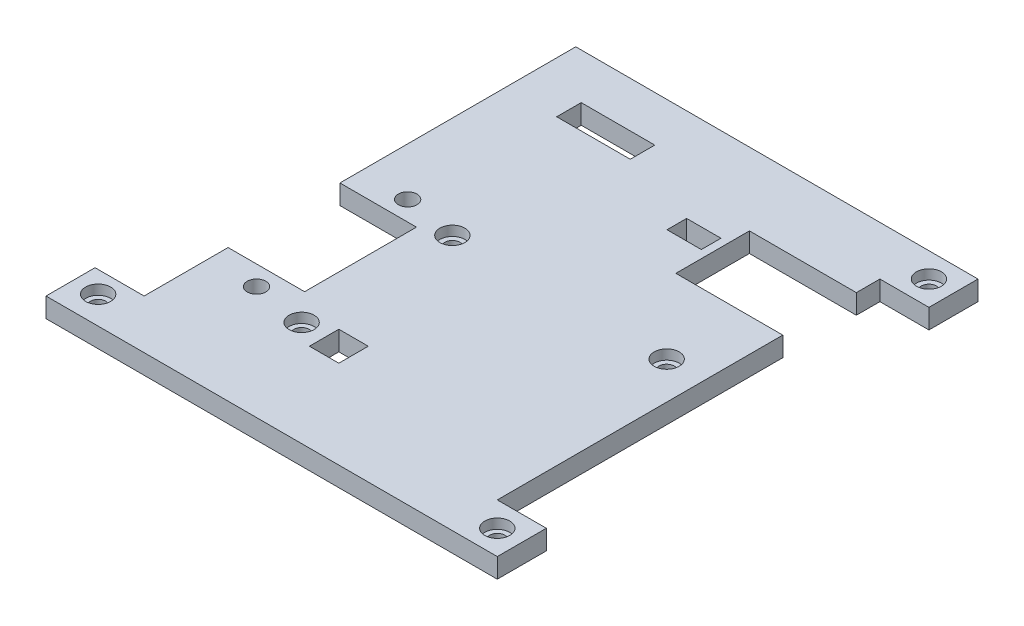
SolidWorks part; units mm, degrees
ref_plane "Спереди" through (0, 0, 0) normal (0, 0, 1) x (1, 0, 0)
ref_plane "Сверху" through (0, 0, 0) normal (0, 1, 0) x (1, 0, 0)
ref_plane "Справа" through (0, 0, 0) normal (1, 0, 0) x (0, 0, -1)
sketch "Sketch1" plane through (0, 0, 0) normal (0, 1, 0) x (1, 0, 0)
  line L0 (32.4854, 9.094) -> (23.5854, 9.094)
  line L1 (0.4854, 14.494) -> (32.4854, 14.494)
  line L2 (0.4854, 14.494) -> (0.4854, -7.5459)
  line L3 (0.4854, -30.506) -> (32.4854, -30.506)
  line L4 (32.4854, 14.494) -> (32.4854, 9.094)
  line L5 (11.3414, -23.5133) -> (14.3414, -23.5133)
  line L6 (11.3414, -23.5133) -> (11.3414, -20.5133)
  line L7 (11.3414, -20.5133) -> (14.3414, -20.5133)
  line L8 (14.3414, -23.5133) -> (14.3414, -20.5133)
  line L9 (23.5854, 9.094) -> (23.5854, 1.594)
  line L10 (23.5854, 1.594) -> (32.4854, 1.594)
  line L11 (32.4854, 1.594) -> (32.4854, -30.506)
  line L12 (0.4854, -18.9459) -> (0.4854, -30.506)
  line L13 (0.4854, -7.5459) -> (6.2854, -7.5459)
  line L15 (0.4854, -18.9459) -> (6.2854, -18.9459)
  line L16 (6.2854, -7.5459) -> (6.2854, -18.9459)
  line L18 (22.7854, 6.994) -> (19.2854, 6.994)
  line L19 (22.7854, 6.994) -> (22.7854, 4.994)
  line L20 (22.7854, 4.994) -> (19.2854, 4.994)
  line L21 (19.2854, 6.994) -> (19.2854, 4.994)
  line L22 (3.6896, 11.844) -> (11.1896, 11.844)
  line L23 (3.6896, 11.844) -> (3.6896, 9.344)
  line L24 (3.6896, 9.344) -> (11.1896, 9.344)
  line L25 (11.1896, 11.844) -> (11.1896, 9.344)
  circle A0 centre (30.6854, -6.439) radius 0.775
  circle A1 centre (8.8414, -6.439) radius 0.775
  circle A2 centre (8.8414, -21.806) radius 0.775
  circle A3 centre (3.3854, -5.5459) radius 0.95
  circle A4 centre (3.3854, -20.9459) radius 0.95
  dimension "D6" = 1.55
  dimension "D16" = 1.9
  dimension "D1" = 45
  dimension "D2" = 32
  dimension "D3" = 1.8
  dimension "D4" = 21.844
  dimension "D5" = 15.367
  dimension "D7" = 8.7
  dimension "D8" = 3
  dimension "D9" = 3
  dimension "D10" = 2.5
  dimension "D11" = 5.4
  dimension "D12" = 7.5
  dimension "D13" = 8.9
  dimension "D14" = 11.4
  dimension "D15" = 5.8
  dimension "D17" = 2
  dimension "D18" = 2
  dimension "D19" = 2.9
  dimension "D20" = 2.9
  dimension "D21" = 0.8
  dimension "D22" = 3.5
  dimension "D23" = 2
  dimension "D24" = 3.4
  dimension "D25" = 7.5
  dimension "D26" = 2.5
  dimension "D27" = 2.65
extrude "Boss-Extrude1" add sketch "Sketch1" along normal blind 2
sketch "Sketch2" plane through (0, 2, 0) normal (0, 1, 0) x (1, 0, 0)
  circle A0 centre (8.8414, -6.439) radius 1.275
  circle A1 centre (30.6854, -6.439) radius 1.275
  circle A2 centre (8.8414, -21.806) radius 1.275
  dimension "D1" = 2.55
extrude "Cut-Extrude1" cut sketch "Sketch2" against normal blind 1
sketch "Sketch4" plane through (0.4854, 0, 0) normal (-1, 0, 0) x (0, 0, 1)
  line L1 (-14.494, 2) -> (7.5459, 2)
  line L2 (-14.494, 2) -> (-14.494, 0)
  line L3 (-14.494, 0) -> (7.5459, 0)
  line L4 (7.5459, 2) -> (7.5459, 0)
  line L5 (18.9459, 0) -> (30.506, 0)
  line L6 (18.9459, 0) -> (18.9459, 2)
  line L7 (18.9459, 2) -> (30.506, 2)
  line L8 (30.506, 0) -> (30.506, 2)
extrude "Boss-Extrude3" add sketch "Sketch4" along normal blind 2
sketch "Sketch5" plane through (32.4854, 0, 0) normal (1, 0, 0) x (0, 0, -1)
  line L1 (14.494, 0) -> (9.094, 0)
  line L2 (14.494, 0) -> (14.494, 2)
  line L3 (14.494, 2) -> (9.094, 2)
  line L4 (9.094, 0) -> (9.094, 2)
  line L5 (1.594, 2) -> (-30.506, 2)
  line L6 (1.594, 2) -> (1.594, 0)
  line L7 (1.594, 0) -> (-30.506, 0)
  line L8 (-30.506, 2) -> (-30.506, 0)
extrude "Boss-Extrude4" add sketch "Sketch5" along normal blind 2
sketch "Sketch6" plane through (0, 0, -14.494) normal (0, 0, -1) x (-1, 0, 0)
  line L1 (-34.4854, 0) -> (1.5146, 0)
  line L2 (-34.4854, 0) -> (-34.4854, 2)
  line L3 (-34.4854, 2) -> (1.5146, 2)
  line L4 (1.5146, 0) -> (1.5146, 2)
extrude "Boss-Extrude5" add sketch "Sketch6" along normal blind 2
sketch "Sketch7" plane through (0, 0, 30.506) normal (0, 0, 1) x (1, 0, 0)
  line L1 (-1.5146, 0) -> (34.4854, 0)
  line L2 (-1.5146, 0) -> (-1.5146, 2)
  line L3 (-1.5146, 2) -> (34.4854, 2)
  line L4 (34.4854, 0) -> (34.4854, 2)
extrude "Boss-Extrude6" add sketch "Sketch7" along normal blind 2
sketch "Sketch8" plane through (34.4854, 0, 0) normal (1, 0, 0) x (0, 0, -1)
  line L0 (9.094, 0) -> (16.494, 0) construction
  line L1 (16.494, 2) -> (11.494, 2)
  line L2 (16.494, 2) -> (16.494, 0)
  line L3 (16.494, 0) -> (11.494, 0)
  line L4 (11.494, 2) -> (11.494, 0)
  line L5 (1.594, 2) -> (-32.506, 2) construction
  line L6 (-32.506, 0) -> (-27.506, 0)
  line L7 (-32.506, 0) -> (-32.506, 2)
  line L8 (-32.506, 2) -> (-27.506, 2)
  line L9 (-27.506, 0) -> (-27.506, 2)
  dimension "D1" = 5
extrude "Boss-Extrude7" add sketch "Sketch8" along normal blind 5
sketch "Sketch9" plane through (-1.5146, 0, 0) normal (-1, 0, 0) x (0, 0, 1)
  line L0 (32.506, 2) -> (18.9459, 2) construction
  line L1 (32.506, 0) -> (27.506, 0)
  line L2 (32.506, 0) -> (32.506, 2)
  line L3 (32.506, 2) -> (27.506, 2)
  line L4 (27.506, 0) -> (27.506, 2)
  dimension "D1" = 5
extrude "Boss-Extrude8" add sketch "Sketch9" along normal blind 5
sketch "Sketch10" plane through (0, 2, 0) normal (0, 1, 0) x (1, 0, 0)
  line L0 (-1.5146, 16.494) -> (39.4854, 16.494) construction
  line L1 (39.4854, 16.494) -> (39.4854, 11.494) construction
  line L2 (39.4854, -27.506) -> (39.4854, -32.506) construction
  line L3 (39.4854, -32.506) -> (-6.5146, -32.506) construction
  line L4 (-6.5146, -32.506) -> (-6.5146, -27.506) construction
  circle A0 centre (36.9854, 13.994) radius 0.775
  circle A1 centre (36.9854, -30.006) radius 0.775
  circle A2 centre (-4.0146, -29.6912) radius 0.775
  dimension "D1" = 1.55
  dimension "D2" = 2.5
  dimension "D3" = 2.5
  dimension "D4" = 2.5
  dimension "D5" = 2.5
  dimension "D6" = 2.5
extrude "Cut-Extrude2" cut sketch "Sketch10" against normal blind 5
sketch "Sketch11" plane through (0, 2, 0) normal (0, 1, 0) x (1, 0, 0)
  circle A0 centre (36.9854, 13.994) radius 1.275
  circle A1 centre (36.9854, -30.006) radius 1.275
  circle A2 centre (-4.0146, -29.6912) radius 1.275
  dimension "D1" = 2.55
extrude "Cut-Extrude3" cut sketch "Sketch11" against normal blind 1
